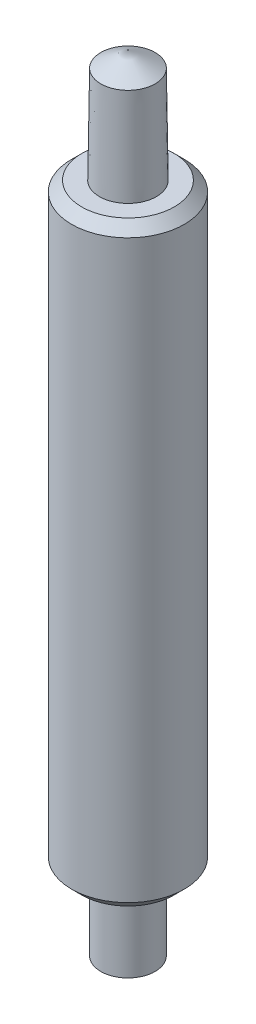
SolidWorks part; units mm, degrees
ref_plane "Alzado" through (0, 0, 0) normal (0, 0, 1) x (1, 0, 0)
ref_plane "Planta" through (0, 0, 0) normal (0, 1, 0) x (1, 0, 0)
ref_plane "Vista lateral" through (0, 0, 0) normal (1, 0, 0) x (0, 0, -1)
ref_plane "Plane1" through (0, 0, 0) normal (0, 0, -1) x (-1, 0, 0)
sketch "Sketch1" plane through (0, 0, 0) normal (0, 0, -1) x (-1, 0, 0)
  line L0 (-0.135, 0.0734) -> (0, 0)
  line L1 (0, 0) -> (0, 3.97)
  line L2 (0, 3.97) -> (-0.135, 3.8921)
  line L3 (-0.135, 3.8921) -> (-0.1415, 3.41)
  line L4 (-0.1415, 3.41) -> (-0.23, 3.41)
  line L5 (-0.23, 3.41) -> (-0.28, 3.36)
  line L6 (-0.28, 3.36) -> (-0.28, 0.5)
  line L7 (-0.28, 0.5) -> (-0.23, 0.45)
  line L8 (-0.23, 0.45) -> (-0.135, 0.45)
  line L9 (-0.135, 0.45) -> (-0.135, 0.0734)
  line L10 (0, 0) -> (0, 3.97) construction
  dimension "D1" = 0.05
  dimension "D2" = 0.1385
  dimension "D3" = 0.145
  dimension "D4" = 0.28
  dimension "D5" = 0.05
  dimension "D6" = 2.91
  dimension "D7" = 2.96
  dimension "D8" = 3.4421
  dimension "D9" = 3.52
  dimension "D10" = 0.3766
  dimension "D11" = 0.45
revolve "Revolve1" add sketch "Sketch1" angle 360 about L10
